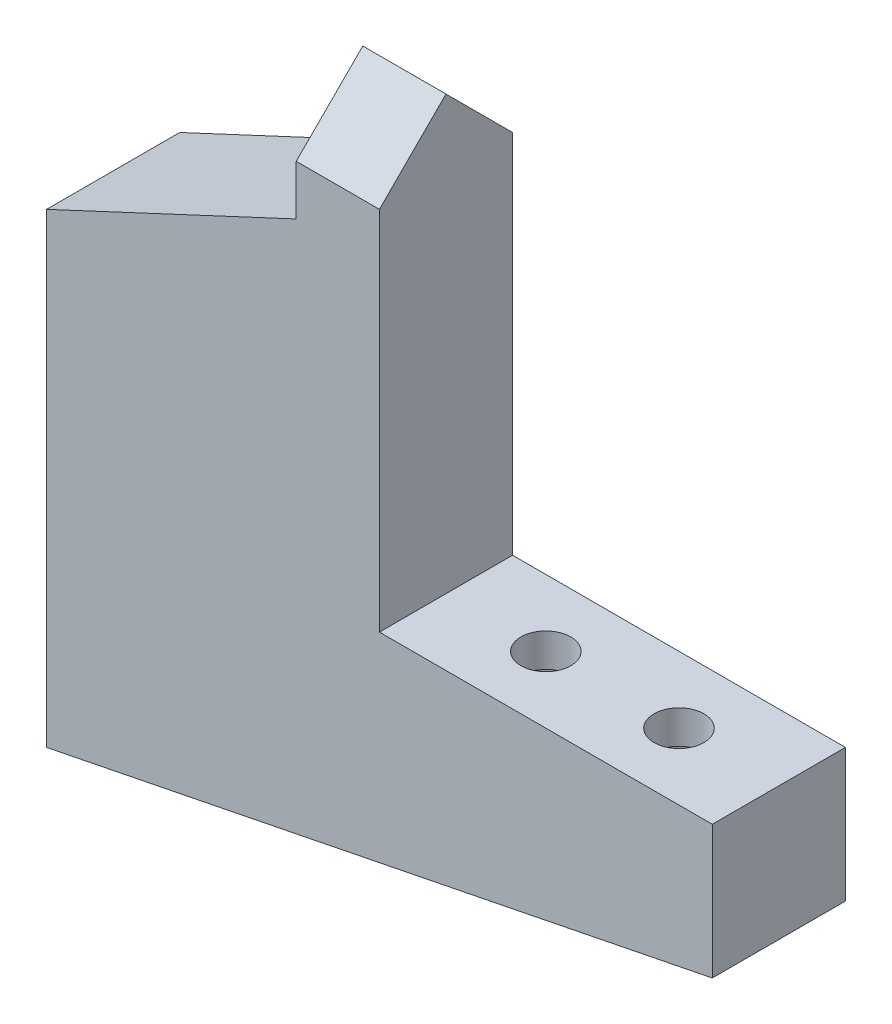
SolidWorks part; units mm, degrees
ref_plane "正面" through (0, 0, 0) normal (0, 0, 1) x (1, 0, 0)
ref_plane "平面" through (0, 0, 0) normal (0, 1, 0) x (1, 0, 0)
ref_plane "右側面" through (0, 0, 0) normal (1, 0, 0) x (0, 0, -1)
sketch "Sketch1" plane through (0, 0, 0) normal (0, 0, 1) x (1, 0, 0)
  line L0 (0, 0) -> (0, 42)
  line L1 (0, 42) -> (20, 42)
  line L2 (20, 42) -> (20, 16)
  line L3 (20, 16) -> (40, 16)
  line L4 (40, 16) -> (40, 8)
  line L5 (40, 8) -> (0, 0)
  point P6 (30, 16)
  dimension "D1" = 26
  dimension "D2" = 20
  dimension "D3" = 20
  dimension "D4" = 8
  dimension "D5" = 42
extrude "Boss-Extrude1" add sketch "Sketch1" along normal blind 8
sketch "Sketch2" plane through (0, 0, 8) normal (0, 0, 1) x (1, 0, 0)
  line L0 (15, 42) -> (15, 35)
  line L1 (20, 42) -> (0, 42) construction
  line L2 (0, 42) -> (0, 0) construction
  line L3 (0, 28) -> (0, 42)
  line L4 (0, 42) -> (15, 42)
  line L5 (15, 35) -> (0, 28)
  dimension "D1" = 14
  dimension "D2" = 7
extrude "Cut-Extrude1" cut sketch "Sketch2" against normal blind 8
sketch "Sketch7" plane through (0, 16, 0) normal (0, 1, 0) x (1, 0, 0)
  line L1 (40, -8) -> (40, 0) construction
  circle A0 centre (34, -4) radius 1.5
  circle A1 centre (26, -4) radius 1.5
  dimension "D1" = 6
  dimension "D2" = 14
extrude "Cut-Extrude4" cut sketch "Sketch7" against normal blind 2
sketch "Sketch9" plane through (0, 14, 0) normal (0, 1, 0) x (1, 0, 0)
  circle A0 centre (34, -4) radius 2.5
  circle A1 centre (26, -4) radius 2.5
extrude "Cut-Extrude5" cut sketch "Sketch9" against normal through all
sketch "Sketch5" plane through (20, 0, 0) normal (1, 0, 0) x (0, 0, -1)
  line L0 (-8, 42) -> (-4, 42)
  line L1 (-8, 42) -> (0, 42) construction
  line L2 (-4, 42) -> (-8, 38)
  line L3 (-8, 16) -> (-8, 42) construction
  line L4 (-8, 38) -> (-8, 42)
  dimension "D1" = 4
  dimension "D2" = 4
extrude "Cut-Extrude2" cut sketch "Sketch5" against normal through all
sketch "Sketch6" plane through (20, 0, 0) normal (1, 0, 0) x (0, 0, -1)
  line L0 (0, 42) -> (-4, 42)
  line L1 (-4, 42) -> (0, 38)
  line L2 (0, 16) -> (0, 42) construction
  line L3 (0, 38) -> (0, 42)
  dimension "D1" = 4
extrude "Cut-Extrude3" cut sketch "Sketch6" against normal through all
hole_wizard "M2x0.4 Tapped Hole1" positions "3DSketch1" profile "Sketch10" tap size "M2x0.4" standard "JIS"
sketch3d "3DSketch1"
  line L0 (0, 28, 0) -> (0, 28, 8) construction
  line L1 (0, 28, 0) -> (0, 0, 0) construction
  point P0 (0, 24, 4)
  point P2 (0, 16, 4)
  point P4 (0, 8, 4)
  dimension "D1" = 4
  dimension "D2" = 12
  dimension "D3" = 20
  dimension "D4" = 4
  dimension "D5" = 4
  dimension "D6" = 4
sketch "Sketch10" plane through (0, 24, 4) normal (0, 1, 0) x (0, 0, 1)
  line L0 (0, 0) -> (0, 8.4807)
  line L1 (0, 8.4807) -> (0.8, 8)
  line L2 (0.8, 8) -> (0.8, 0)
  line L5 (0.8, 0) -> (0, 0)
  line L10 (0, 8.4807) -> (-0.8, 8) construction
  line L11 (0, -6.35) -> (0, 107.95) construction
  dimension "Tap Drill Dia." = 1.6
  dimension "Tap Drill Depth" = 8
  dimension "Drill Angle" = 118
cosmetic thread "Hole Thread1" parameters "D1"=7, "D2"=2
cosmetic thread "Hole Thread2" parameters "D1"=7, "D2"=2
cosmetic thread "Hole Thread3" parameters "D1"=7, "D2"=2
